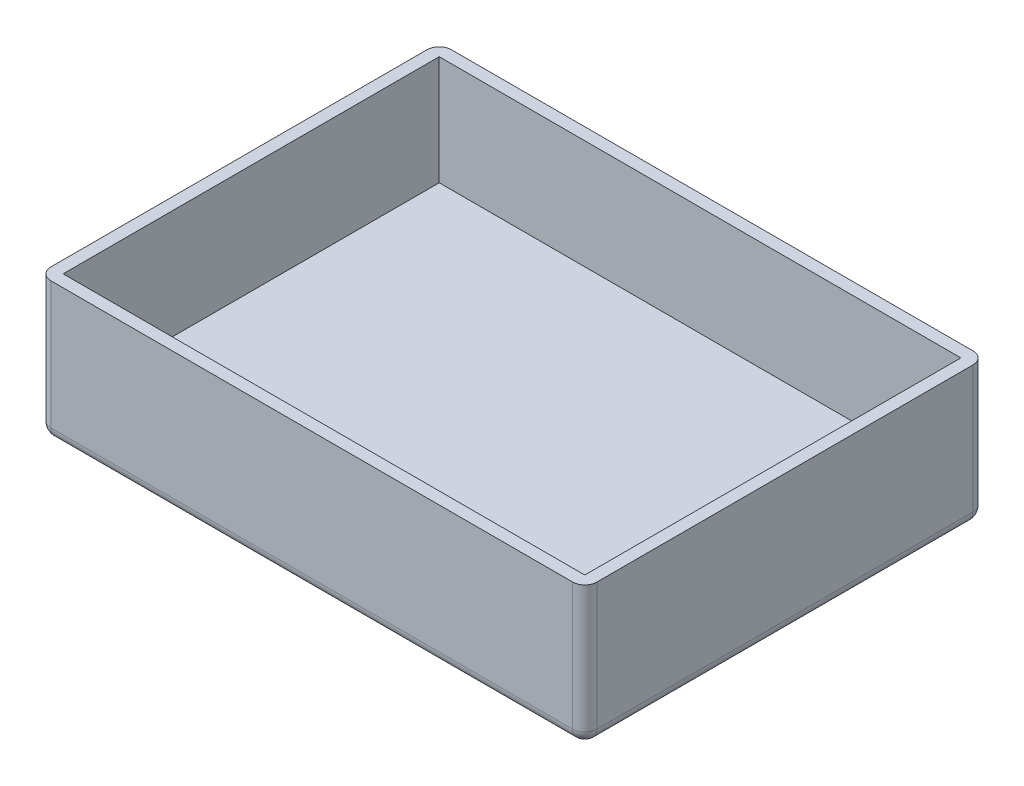
SolidWorks part; units mm, degrees
material "Glass"
ref_plane "Front Plane" through (0, 0, 0) normal (0, 0, 1) x (1, 0, 0)
ref_plane "Top Plane" through (0, 0, 0) normal (0, 1, 0) x (1, 0, 0)
ref_plane "Right Plane" through (0, 0, 0) normal (1, 0, 0) x (0, 0, -1)
sketch "Sketch1" plane through (0, 0, 0) normal (0, 1, 0) x (1, 0, 0)
  line L1 (-62.8276, -33.4344) -> (387.1724, -33.4344)
  line L2 (-62.8276, -33.4344) -> (-62.8276, 296.5656)
  line L3 (-62.8276, 296.5656) -> (387.1724, 296.5656)
  line L4 (387.1724, -33.4344) -> (387.1724, 296.5656)
  dimension "D1" = 450
  dimension "D2" = 330
extrude "Boss-Extrude1" add sketch "Sketch1" along normal blind 115
sketch "Sketch2" plane through (0, 115, 0) normal (0, 1, 0) x (1, 0, 0)
  line L0 (-62.8276, 296.5656) -> (-62.8276, -33.4344) construction
  line L1 (-52.8276, 286.5656) -> (377.1724, 286.5656)
  line L2 (-52.8276, 286.5656) -> (-52.8276, -23.4344)
  line L3 (-52.8276, -23.4344) -> (377.1724, -23.4344)
  line L4 (377.1724, 286.5656) -> (377.1724, -23.4344)
  line L5 (-62.8276, -33.4344) -> (387.1724, -33.4344) construction
  dimension "D1" = 430
  dimension "D2" = 310
  dimension "D3" = 10
  dimension "D4" = 10
extrude "Cut-Extrude1" cut sketch "Sketch2" against normal blind 90
fillet "Fillet1" radius 10 8 edges at (162.1724, 0, 33.4344) (387.1724, 0, -131.5656) (162.1724, 0, -296.5656) (-62.8276, 0, -131.5656) (-62.8276, 57.5, 33.4344) (-62.8276, 57.5, -296.5656) (387.1724, 57.5, -296.5656) (387.1724, 57.5, 33.4344)
